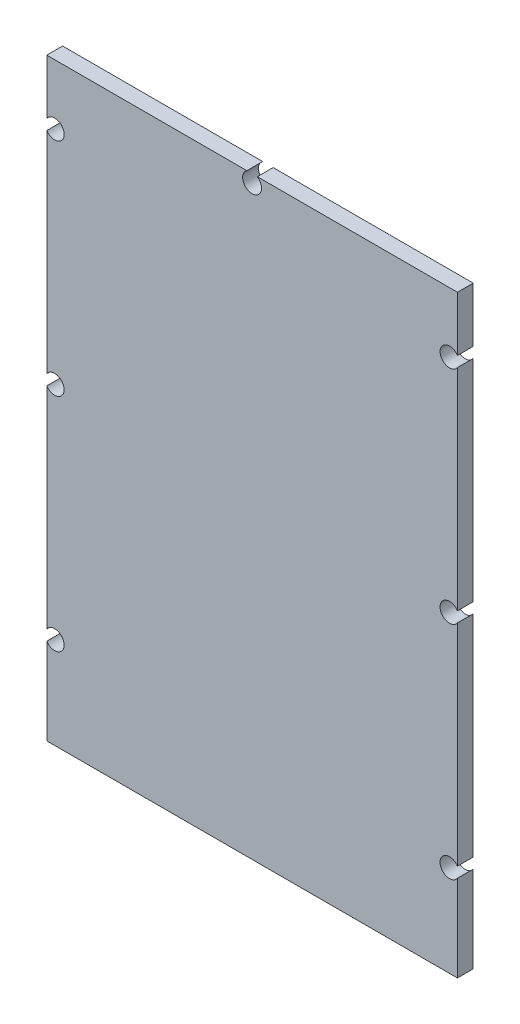
SolidWorks part; units mm, degrees
ref_plane "Front Plane" through (0, 0, 0) normal (0, 0, 1) x (1, 0, 0)
ref_plane "Top Plane" through (0, 0, 0) normal (0, 1, 0) x (1, 0, 0)
ref_plane "Right Plane" through (0, 0, 0) normal (1, 0, 0) x (0, 0, -1)
sketch "Sketch1" plane through (0, 0, 0) normal (0, 0, 1) x (1, 0, 0)
  line L1 (-32.5, 47) -> (32.5, 47)
  line L2 (-32.5, 47) -> (-32.5, -47)
  line L3 (-32.5, -47) -> (32.5, -47)
  line L4 (32.5, 47) -> (32.5, -47)
  point P4 (0, 47)
  point P6 (-32.5, 0)
  dimension "D1" = 65
  dimension "D2" = 94
extrude "Boss-Extrude1" add sketch "Sketch1" along normal blind 2.5
sketch "Sketch2" plane through (0, 0, 0) normal (0, 0, 1) x (1, 0, 0)
  line L0 (32.5, 47) -> (-32.5, 47) construction
  line L1 (-32.5, 47) -> (-32.5, -47) construction
  line L2 (0, 47) -> (0, -47) construction
  line L3 (-32.5, -47) -> (32.5, -47) construction
  circle A0 centre (-31.25, 37.5) radius 1.5
  circle A1 centre (31.25, 37.5) radius 1.5
  dimension "D1" = 3
  dimension "D2" = 9.5
  dimension "D3" = 1.25
extrude "Cut-Extrude1" cut sketch "Sketch2" along normal through all both and the other way through all
pattern_linear "LPattern1" count 3 spacing 35 along (0, -1, 0) of "Cut-Extrude1"
sketch "Sketch3" plane through (0, 0, 0) normal (0, 0, 1) x (1, 0, 0)
  line L0 (32.5, 47) -> (-32.5, 47) construction
  circle A0 centre (0, 45.75) radius 1.5
  dimension "D1" = 3
  dimension "D2" = 1.25
extrude "Cut-Extrude2" cut sketch "Sketch3" along normal through all both and the other way through all
equation "\"wall\"=2.5"
equation "\"D1@Sketch1\"=\"wall\"*2+60"
equation "\"D2@Sketch1\"=\"wall\"*2+89"
equation "\"screw\"=3"
equation "\"D1@Sketch2\"=\"screw\""
equation "\"D2@Sketch2\"=\"wall\"+7"
equation "\"D3@Sketch2\"=\"wall\"/2"
equation "\"D1@Sketch3\"=\"screw\""
equation "\"D2@Sketch3\"=\"wall\"/2"
